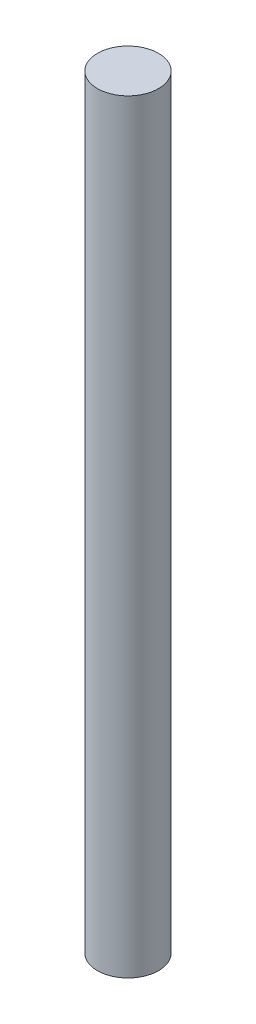
SolidWorks part; units mm, degrees
ref_plane "Front Plane" through (0, 0, 0) normal (0, 0, 1) x (1, 0, 0)
ref_plane "Top Plane" through (0, 0, 0) normal (0, 1, 0) x (1, 0, 0)
ref_plane "Right Plane" through (0, 0, 0) normal (1, 0, 0) x (0, 0, -1)
sketch "Sketch1" plane through (0, 0, 0) normal (0, 1, 0) x (1, 0, 0)
  circle A0 centre (-0.0278, 0) radius 0.508
  dimension "D1" = 1.016
extrude "Boss-Extrude1" add sketch "Sketch1" along normal blind 12.7
